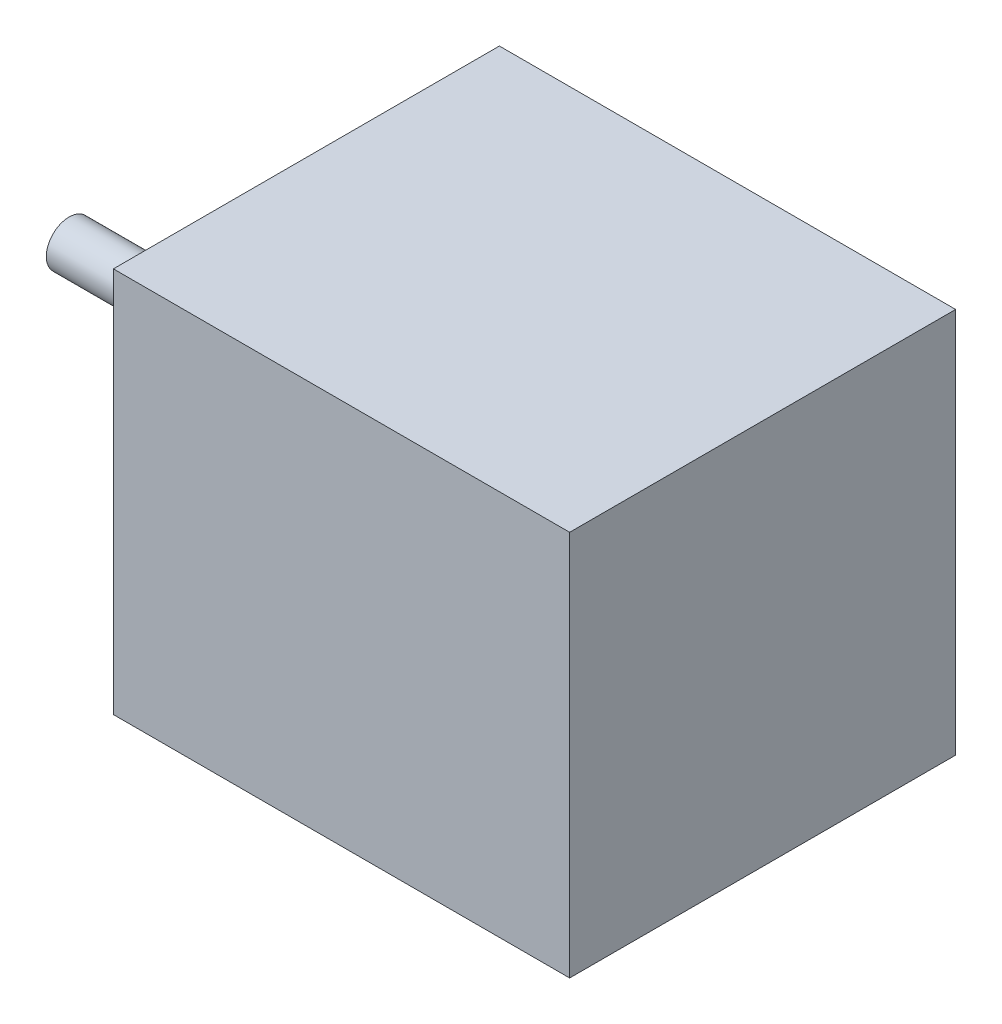
SolidWorks part; units mm, degrees
ref_plane "Front Plane" through (0, 0, 0) normal (0, 0, 1) x (1, 0, 0)
ref_plane "Top Plane" through (0, 0, 0) normal (0, 1, 0) x (1, 0, 0)
ref_plane "Right Plane" through (0, 0, 0) normal (1, 0, 0) x (0, 0, -1)
sketch "Sketch1" plane through (0, 0, 0) normal (1, 0, 0) x (0, 0, -1)
  line L1 (-21.15, 21.15) -> (21.15, 21.15)
  line L2 (-21.15, 21.15) -> (-21.15, -21.15)
  line L3 (-21.15, -21.15) -> (21.15, -21.15)
  line L4 (21.15, 21.15) -> (21.15, -21.15)
  line L5 (-21.15, 21.15) -> (21.15, -21.15) construction
  line L6 (-21.15, -21.15) -> (21.15, 21.15) construction
  point P0 (0, 0)
  dimension "D1" = 42.3
  dimension "D2" = 42.3
extrude "Boss-Extrude1" add sketch "Sketch1" along normal blind 50
sketch "Sketch2" plane through (0, 0, 0) normal (1, 0, 0) x (0, 0, -1)
  circle A0 centre (0, 0) radius 11
  dimension "D1" = 22
extrude "Boss-Extrude2" add sketch "Sketch2" against normal blind 2
sketch "Sketch3" plane through (0, 0, 0) normal (1, 0, 0) x (0, 0, -1)
  circle A0 centre (0, 0) radius 2.5
  dimension "D1" = 5
extrude "Boss-Extrude3" add sketch "Sketch3" against normal blind 24 from surface at -2 starting at face at (-2, 0, -11)
sketch "Sketch4" plane through (0, 0, 0) normal (1, 0, 0) x (0, 0, -1)
  line L0 (0, 24.2597) -> (0, -24.6388) construction
  line L1 (0, 23.265) -> (0, -23.265) construction
  line L2 (25.6496, 0) -> (-27.9871, 0) construction
  line L3 (23.265, 0) -> (-23.265, 0) construction
  circle A0 centre (15.5, 16.5) radius 2
  circle A1 centre (15.5, -16.5) radius 2
  circle A2 centre (-15.5, -16.5) radius 2
  circle A3 centre (-15.5, 16.5) radius 2
  dimension "D1" = 4
  dimension "D2" = 31
extrude "Cut-Extrude1" cut sketch "Sketch4" along normal blind 4.5
